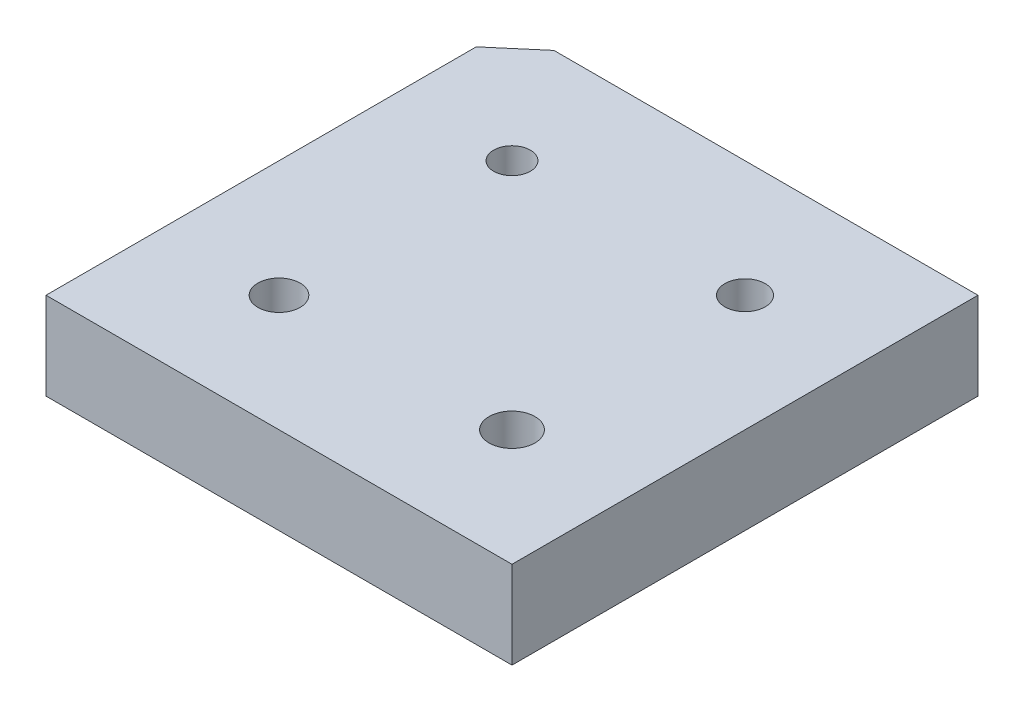
SolidWorks part; units mm, degrees
ref_plane "Front Plane" through (0, 0, 0) normal (0, 0, 1) x (1, 0, 0)
ref_plane "Top Plane" through (0, 0, 0) normal (0, 1, 0) x (1, 0, 0)
ref_plane "Right Plane" through (0, 0, 0) normal (1, 0, 0) x (0, 0, -1)
sketch "Sketch1" plane through (0, 0, 0) normal (0, 1, 0) x (1, 0, 0)
  line L1 (-25.4, -25.4) -> (25.4, -25.4)
  line L2 (-25.4, -25.4) -> (-25.4, 25.4)
  line L3 (-25.4, 25.4) -> (25.4, 25.4)
  line L4 (25.4, -25.4) -> (25.4, 25.4)
  line L5 (-25.4, -25.4) -> (25.4, 25.4) construction
  line L6 (-25.4, 25.4) -> (25.4, -25.4) construction
  point P0 (0, 0)
  dimension "D1" = 50.8
  dimension "D2" = 50.8
extrude "Boss-Extrude1" add sketch "Sketch1" along normal blind 4.7625
sketch "Sketch2" plane through (0, 4.7625, 0) normal (0, 1, 0) x (1, 0, 0)
  line L1 (12.7, -12.7) -> (-12.7, -12.7)
  line L2 (12.7, -12.7) -> (12.7, 12.7)
  line L3 (12.7, 12.7) -> (-12.7, 12.7)
  line L4 (-12.7, -12.7) -> (-12.7, 12.7)
  line L5 (12.7, -12.7) -> (-12.7, 12.7) construction
  line L6 (12.7, 12.7) -> (-12.7, -12.7) construction
  line L7 (25.4, -25.4) -> (-25.4, -25.4)
  line L8 (25.4, -25.4) -> (25.4, 25.4)
  line L9 (25.4, 25.4) -> (-25.4, 25.4)
  line L10 (-25.4, -25.4) -> (-25.4, 25.4)
  line L11 (25.4, -25.4) -> (-25.4, 25.4) construction
  line L12 (25.4, 25.4) -> (-25.4, -25.4) construction
  circle A0 centre (-6.35, 6.35) radius 1.0008
  circle A1 centre (6.35, 6.35) radius 1.0998
  circle A2 centre (-6.35, -6.35) radius 1.1506
  circle A3 centre (6.35, -6.35) radius 1.2497
  point P8 (0, 0)
  point P14 (0, 0)
  point P21 (1.9305, 1.9305)
  line M5 (25.4, -25.4) -> (25.4, 25.4)
  line M6 (25.4, 25.4) -> (-25.4, 25.4)
  line M7 (-25.4, 25.4) -> (-25.4, -25.4)
  line M8 (-25.4, -25.4) -> (25.4, -25.4)
  dimension "D9" = 2.0015
  dimension "D10" = 2.1996
  dimension "D11" = 6.35
  dimension "D12" = 2.4994
  dimension "D2" = 2.3012
  dimension "D3" = 25.4
  dimension "D4" = 25.4
  dimension "D5" = 6.35
  dimension "D6" = 6.35
  dimension "D7" = 6.35
  dimension "D8" = 6.35
  dimension "D13" = 6.35
  dimension "D14" = 6.35
  dimension "D15" = 6.35
extrude "Cut-Extrude1" cut sketch "Sketch2" against normal through all contours L1 L4 L3 L2 M8 M5 M6 M7 | A0 | A1 | A2 | A3
sketch "Sketch3" plane through (0, 4.7625, 0) normal (0, 1, 0) x (1, 0, 0)
  line L1 (-12.7, -12.7) -> (-12.7, 12.7) construction
  line L3 (12.7, 12.7) -> (-12.7, 12.7) construction
  line L4 (-10.4141, 12.7) -> (-12.7, 12.7)
  line L5 (-12.7, 12.7) -> (-12.7, 10.7506)
  line L6 (-12.7, 10.7506) -> (-10.4141, 12.7)
extrude "Cut-Extrude2" cut sketch "Sketch3" against normal through all
